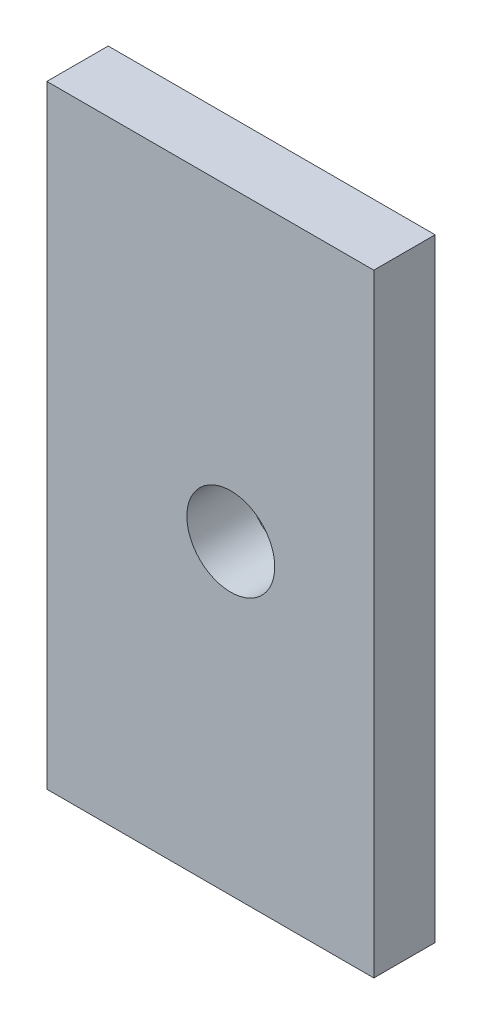
SolidWorks part; units mm, degrees
material "Plain Carbon Steel"
ref_plane "Front Plane" through (0, 0, 0) normal (0, 0, 1) x (1, 0, 0)
ref_plane "Top Plane" through (0, 0, 0) normal (0, 1, 0) x (1, 0, 0)
ref_plane "Right Plane" through (0, 0, 0) normal (1, 0, 0) x (0, 0, -1)
sketch "Sketch1" plane through (0, 0, 0) normal (0, 0, 1) x (1, 0, 0)
  line L1 (0, 0) -> (-16, 0)
  line L2 (0, 0) -> (0, 30)
  line L3 (0, 30) -> (-16, 30)
  line L4 (-16, 0) -> (-16, 30)
  dimension "D1" = 16
  dimension "D2" = 30
extrude "Boss-Extrude1" add sketch "Sketch1" along normal blind 3
hole_wizard "M4 Clearance Hole1" positions "Sketch3" profile "Sketch2" hole size "M4" standard "ISO"
sketch "Sketch3" plane through (0, 0, 3) normal (0, 0, 1) x (1, 0, 0)
  line L0 (0, 0) -> (0, 30) construction
  line L1 (0, 30) -> (-16, 30) construction
  point P0 (-7, 15)
  dimension "D1" = 7
  dimension "D2" = 15
sketch "Sketch2" plane through (-7, 15, 3) normal (1, 0, 0) x (0, -1, 0)
  line L0 (0, 0) -> (0, 101.2919)
  line L1 (0, 101.2919) -> (2.15, 100)
  line L2 (2.15, 100) -> (2.15, 0)
  line L5 (2.15, 0) -> (0, 0)
  line L10 (0, 101.2919) -> (-2.15, 100) construction
  line L11 (0, -6.35) -> (0, 107.95) construction
  dimension "Hole Dia." = 4.3
  dimension "Hole Depth" = 100
  dimension "Drill Angle" = 118
